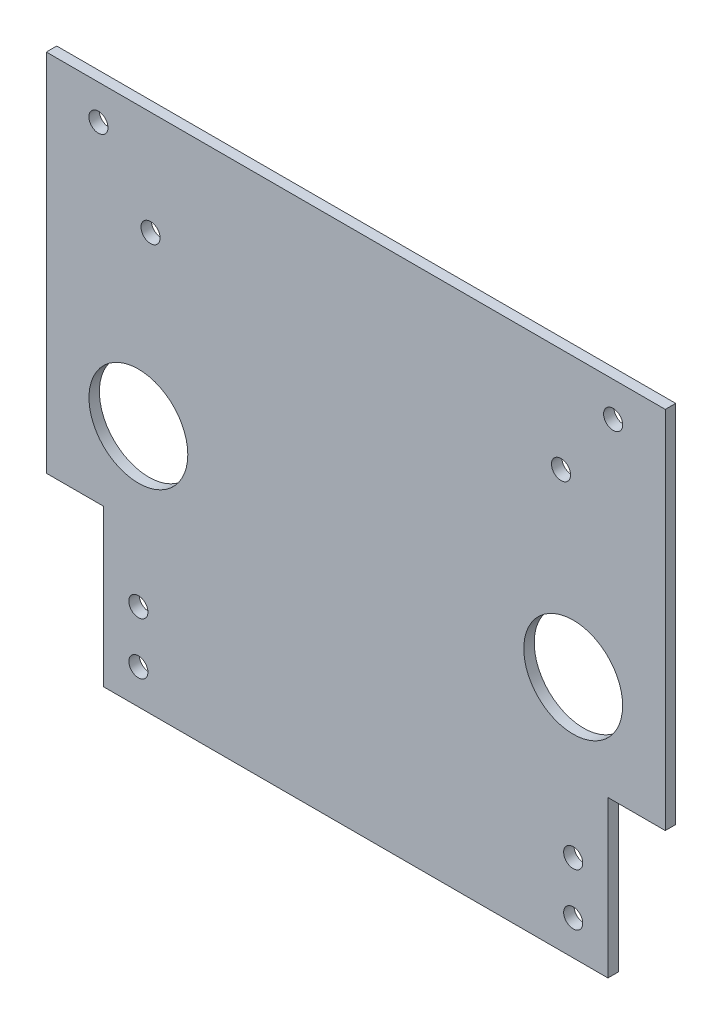
SolidWorks part; units mm, degrees
ref_plane "Front Plane" through (0, 0, 0) normal (0, 0, 1) x (1, 0, 0)
ref_plane "Top Plane" through (0, 0, 0) normal (0, 1, 0) x (1, 0, 0)
ref_plane "Right Plane" through (0, 0, 0) normal (1, 0, 0) x (0, 0, -1)
sketch "Sketch1" plane through (0, 0, 0) normal (0, 0, 1) x (1, 0, 0)
  line L1 (0, 0) -> (178.16, 0)
  line L2 (0, 0) -> (0, -150)
  line L3 (0, -150) -> (178.16, -150)
  line L4 (178.16, 0) -> (178.16, -150)
  dimension "D1" = 150
  dimension "D2" = 178.16
extrude "Boss-Extrude1" add sketch "Sketch1" along normal blind 3
sketch "Sketch2" plane through (0, 0, 3) normal (0, 0, 1) x (1, 0, 0)
  line L0 (0, 0) -> (0, -150) construction
  line L1 (178.16, -150) -> (178.16, 0) construction
  line L2 (0, -150) -> (178.16, -150) construction
  line L3 (178.16, 0) -> (0, 0) construction
  circle A0 centre (26.5, -80) radius 14.225
  circle A1 centre (151.66, -80) radius 14.225
  circle A3 centre (26.5, -140) radius 2.75
  circle A4 centre (151.66, -140) radius 2.75
  circle A8 centre (26.5, -125) radius 2.75
  circle A9 centre (151.66, -125) radius 2.75
  dimension "D1" = 28.45
  dimension "D2" = 28.45
  dimension "D3" = 10
  dimension "D4" = 5.5
  dimension "D7" = 5.5
  dimension "D14" = 5.5
  dimension "D17" = 5.5
  dimension "D9" = 26.5
  dimension "D10" = 26.5
  dimension "D12" = 80
  dimension "D15" = 15
  dimension "D16" = 15
extrude "Cut-Extrude1" cut sketch "Sketch2" against normal through all
sketch "Sketch4" plane through (0, 0, 3) normal (0, 0, 1) x (1, 0, 0)
  line L1 (16.5, -150) -> (16.5, -105)
  line L2 (16.5, -105) -> (0, -105)
  line L3 (0, 0) -> (0, -150) construction
  line L4 (0, -105) -> (0, -150)
  line L5 (0, -150) -> (16.5, -150)
  line L6 (0, -150) -> (178.16, -150) construction
  line L8 (178.16, -150) -> (161.66, -150)
  line L9 (178.16, -150) -> (178.16, -105)
  line L10 (178.16, -105) -> (161.66, -105)
  line L11 (161.66, -150) -> (161.66, -105)
  dimension "D1" = 45
  dimension "D2" = 16.5
  dimension "D3" = 16.5
  dimension "D4" = 45
extrude "Cut-Extrude3" cut sketch "Sketch4" against normal through all
sketch "Sketch5" plane through (0, 0, 3) normal (0, 0, 1) x (1, 0, 0)
  line L0 (178.16, 0) -> (0, 0) construction
  line L1 (178.16, -105) -> (178.16, 0) construction
  line L2 (0, 0) -> (0, -105) construction
  circle A0 centre (163.16, -10) radius 2.75
  circle A1 centre (15, -10) radius 2.75
  circle A3 centre (148.16, -30) radius 2.75
  circle A4 centre (30, -30) radius 2.75
  dimension "D3" = 5.5
  dimension "D4" = 5.5
  dimension "D5" = 5.5
  dimension "D6" = 5.5
  dimension "D1" = 10
  dimension "D2" = 30
  dimension "D7" = 15
  dimension "D8" = 15
  dimension "D9" = 30
  dimension "D10" = 30
extrude "Cut-Extrude4" cut sketch "Sketch5" against normal through all
